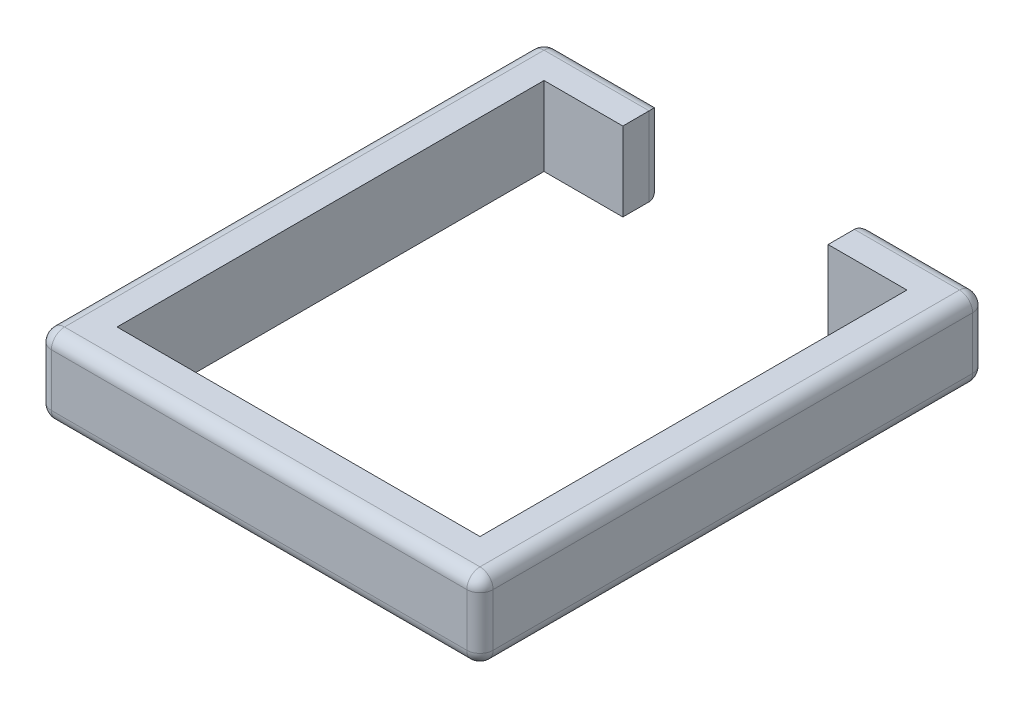
SolidWorks part; units mm, degrees
ref_plane "Front Plane" through (0, 0, 0) normal (0, 0, 1) x (1, 0, 0)
ref_plane "Top Plane" through (0, 0, 0) normal (0, 1, 0) x (1, 0, 0)
ref_plane "Right Plane" through (0, 0, 0) normal (1, 0, 0) x (0, 0, -1)
sketch "Sketch1" plane through (0, 0, 0) normal (0, 1, 0) x (1, 0, 0)
  line L0 (228.6, 0) -> (0, 0)
  line L1 (0, 0) -> (0, -977.9)
  line L2 (0, -977.9) -> (854.075, -977.9)
  line L3 (854.075, -977.9) -> (854.075, 0)
  line L4 (854.075, 0) -> (625.475, 0)
  line L5 (625.475, 0) -> (625.475, -76.2)
  line L6 (625.475, -76.2) -> (777.875, -76.2)
  line L7 (777.875, -76.2) -> (777.875, -901.7)
  line L8 (777.875, -901.7) -> (76.2, -901.7)
  line L9 (76.2, -901.7) -> (76.2, -76.2)
  line L10 (76.2, -76.2) -> (228.6, -76.2)
  line L11 (228.6, -76.2) -> (228.6, 0)
  dimension "D1" = 825.5
  dimension "D2" = 76.2
  dimension "D3" = 76.2
  dimension "D4" = 76.2
  dimension "D5" = 701.675
  dimension "D6" = 152.4
extrude "Boss-Extrude1" add sketch "Sketch1" along normal blind 152.4
fillet "Fillet1" radius 25.4 16 edges at (427.0375, 152.4, 977.9) (427.0375, 0, 977.9) (739.775, 152.4, 0) (625.475, 76.2, 0) (739.775, 0, 0) (228.6, 76.2, 0) (114.3, 152.4, 0) (114.3, 0, 0) (0, 76.2, 0) (0, 152.4, 488.95) (0, 76.2, 977.9) (0, 0, 488.95) (854.075, 76.2, 977.9) (854.075, 152.4, 488.95) (854.075, 76.2, 0) (854.075, 0, 488.95)
